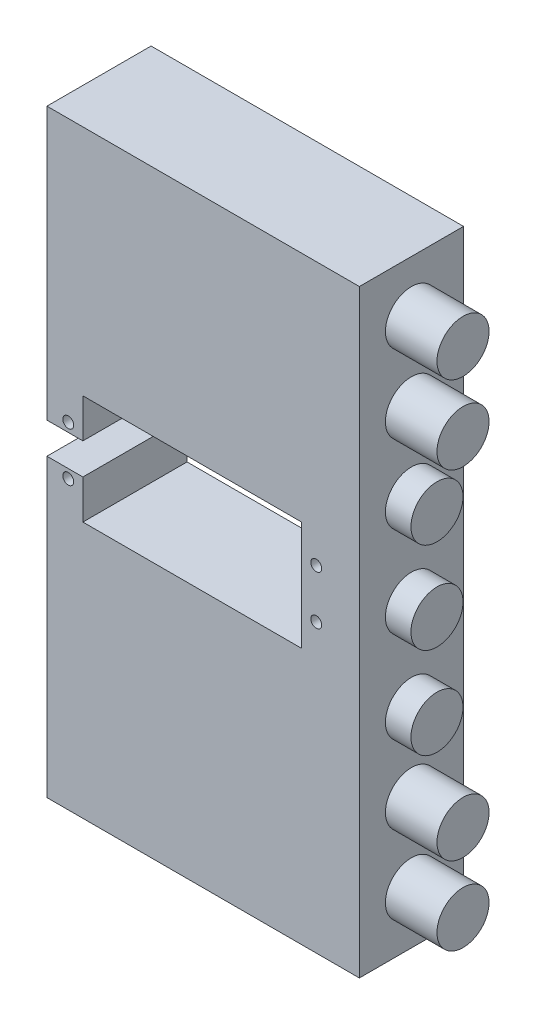
SolidWorks part; units mm, degrees
ref_plane "前基準面" through (0, 0, 0) normal (0, 0, 1) x (1, 0, 0)
ref_plane "上基準面" through (0, 0, 0) normal (0, 1, 0) x (1, 0, 0)
ref_plane "右基準面" through (0, 0, 0) normal (1, 0, 0) x (0, 0, -1)
sketch "草圖1" plane through (0, 0, 0) normal (0, 0, 1) x (1, 0, 0)
  line L0 (55, -3) -> (115, -3) construction
  line L5 (85, 54.5) -> (85, -60.5) construction
  line L6 (55, -3) -> (55, 0)
  line L7 (55, 0) -> (62, 0)
  line L8 (62, 0) -> (62, 7.5)
  line L9 (62, 7.5) -> (104, 7.5)
  line L10 (104, 7.5) -> (104, -13.5)
  line L11 (55, -6) -> (62, -6)
  line L12 (62, -6) -> (62, -13.5)
  line L13 (62, -13.5) -> (104, -13.5)
  line L14 (55, -3) -> (55, -6)
  circle A0 centre (59.19, 1.7) radius 1.05
  circle A1 centre (106.81, 1.7) radius 1.05
  circle A2 centre (106.81, -7.7) radius 1.05
  circle A3 centre (59.19, -7.7) radius 1.05
  point P18 (104, -3)
  dimension "D9" = 2.1
  dimension "D10" = 2.1
  dimension "D3" = 7
  dimension "D4" = 42
  dimension "D5" = 6
  dimension "D6" = 10.5
  dimension "D7" = 2.81
  dimension "D8" = 5.8
  dimension "D11" = 5.8
  dimension "D12" = 2.81
sketch "草圖5" plane through (0, 0, 0) normal (0, 0, 1) x (1, 0, 0)
  line L1 (55.0953, 52.2229) -> (115.0953, 52.2229)
  line L2 (55.0953, 52.2229) -> (55.0953, -62.7771)
  line L3 (55.0953, -62.7771) -> (115.0953, -62.7771)
  line L4 (115.0953, 52.2229) -> (115.0953, -62.7771)
  dimension "D1" = 115
  dimension "D2" = 60
extrude "填料-伸長2" add sketch "草圖5" along normal blind 20
extrude "除料-伸長4" cut sketch "草圖1" along normal blind 20 contours L12 L13 L10 L9 L8 L7 L6 L14 L11 | A1 | A2 | A3 | A0
ref_plane "平面1" through (115, 0, 0) normal (1, 0, 0) x (0, 0, -1)
sketch "草圖6" plane through (115, 0, 0) normal (1, 0, 0) x (0, 0, -1)
  line L0 (-20, -5.2771) -> (0, -5.2771) construction
  line L1 (-20, -62.7771) -> (-20, 52.2229) construction
  line L2 (0, -62.7771) -> (0, 52.2229) construction
  line L3 (-10, 52.2229) -> (-10, -62.7771) construction
  line L4 (-20, 52.2229) -> (0, 52.2229) construction
  line L5 (-20, -62.7771) -> (0, -62.7771) construction
  circle A0 centre (-10, 42.2229) radius 5
  circle A1 centre (-10, 27.2229) radius 5
  circle A2 centre (-10, -37.7771) radius 5
  circle A3 centre (-10, -52.7771) radius 5
  dimension "D1" = 10
  dimension "D2" = 10
  dimension "D3" = 5
  dimension "D4" = 5
sketch "草圖7" plane through (115, 0, 0) normal (1, 0, 0) x (0, 0, -1)
  line L0 (-20, -5.2771) -> (0, -5.2771) construction
  line L1 (-10, 52.2229) -> (-10, -62.7771) construction
  circle A0 centre (-10, 12.2229) radius 5
  circle A1 centre (-10, -5.2771) radius 5
  circle A2 centre (-10, -22.7771) radius 5
  circle A3 centre (-10, 27.2229) radius 5 construction
  dimension "D1" = 10
  dimension "D2" = 5
extrude "填料-伸長3" add sketch "草圖6" along normal blind 10
extrude "填料-伸長4" add sketch "草圖7" along normal blind 5
